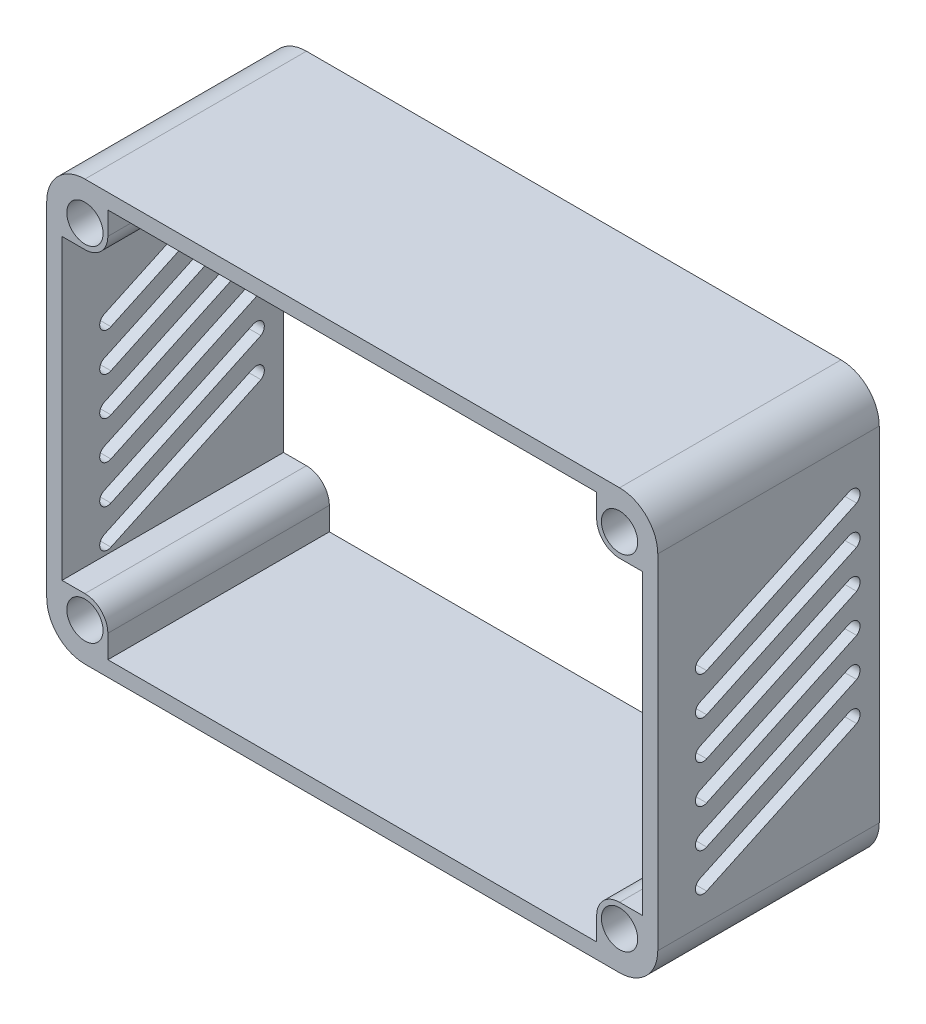
SolidWorks part; units mm, degrees
material "ABS"
ref_plane "Спереди" through (0, 0, 0) normal (0, 0, 1) x (1, 0, 0)
ref_plane "Сверху" through (0, 0, 0) normal (0, 1, 0) x (1, 0, 0)
ref_plane "Справа" through (0, 0, 0) normal (1, 0, 0) x (0, 0, -1)
sketch "Эскиз1" plane through (0, 0, 0) normal (0, 0, 1) x (1, 0, 0)
  line L0 (-70, 55) -> (70, 55)
  line L1 (80, 45) -> (80, -45)
  line L2 (70, -55) -> (-70, -55)
  line L3 (-80, -45) -> (-80, 45)
  line L4 (-64, 51) -> (64, 51)
  line L5 (-64, -51) -> (64, -51)
  line L6 (76, -39) -> (76, 39)
  line L7 (-76, 39) -> (-76, -39)
  line L8 (-70, 39) -> (-76, 39)
  line L9 (-64, 45) -> (-64, 51)
  line L10 (64, 45) -> (64, 51)
  line L11 (70, 39) -> (76, 39)
  line L12 (70, -39) -> (76, -39)
  line L13 (64, -45) -> (64, -51)
  line L14 (-64, -45) -> (-64, -51)
  line L15 (-70, -39) -> (-76, -39)
  arc A0 (-70, 55) -> (-80, 45) centre (-70, 45) ccw
  arc A1 (80, 45) -> (70, 55) centre (70, 45) ccw
  arc A2 (70, -55) -> (80, -45) centre (70, -45) ccw
  arc A3 (-80, -45) -> (-70, -55) centre (-70, -45) ccw
  arc A4 (-70, 39) -> (-64, 45) centre (-70, 45) ccw
  arc A5 (64, 45) -> (70, 39) centre (70, 45) ccw
  arc A6 (70, -39) -> (64, -45) centre (70, -45) ccw
  arc A7 (-64, -45) -> (-70, -39) centre (-70, -45) ccw
  circle A8 centre (70, 45) radius 4.75
  circle A9 centre (70, -45) radius 4.75
  circle A10 centre (-70, -45) radius 4.75
  circle A11 centre (-70, 45) radius 4.75
  dimension "D1" = 12
  dimension "D2" = 9.5
extrude "Бобышка-Вытянуть1" add sketch "Эскиз1" along normal blind 58
sketch "Эскиз2" plane through (-80, 0, 0) normal (-1, 0, 0) x (0, 0, 1)
  line L0 (7.1655, 32.1331) -> (45.3847, 32.1331) construction
  line L1 (7.1655, 32.1331) -> (35.3934, 18.9702) construction
  line L3 (46.938, 15.8642) -> (8.0503, 33.9955)
  line L4 (45.1935, 12.1231) -> (5.9162, 30.4716)
  arc A0 (45.1935, 12.1231) -> (46.9378, 15.8643) centre (46.0657, 13.9936) ccw
  arc A1 (8.0503, 33.9955) -> (5.9162, 30.4716) centre (7.0945, 32.1662) ccw
  point P9 (46.0657, 13.9936)
  point P11 (5.0798, 29.8861)
  point P12 (5.9162, 30.4716)
  dimension "D2" = 43
  dimension "D1" = 25
extrude "Вырез-Вытянуть1" cut sketch "Эскиз2" against normal blind 169 contours L3 A1 L4 A0
pattern_linear "Линейный массив1" count 6 spacing 10 along (0, -1, 0) of "Вырез-Вытянуть1"
